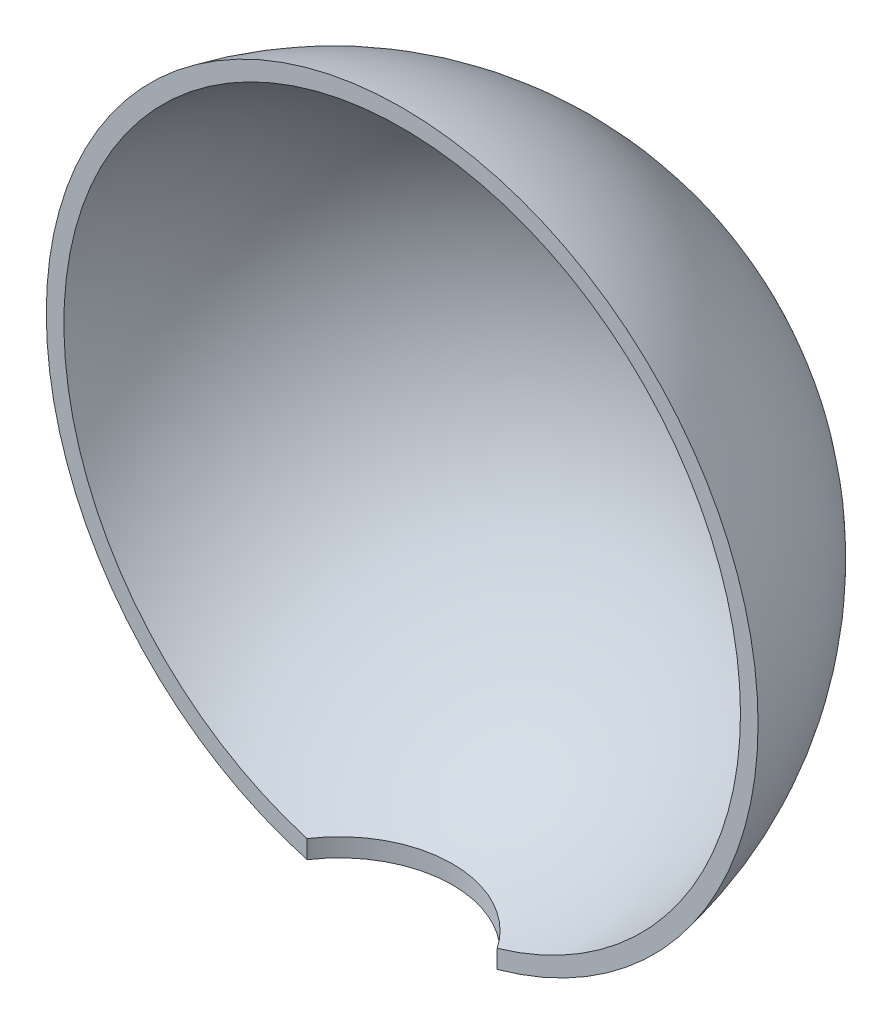
SolidWorks part; units mm, degrees
ref_plane "Front Plane" through (0, 0, 0) normal (0, 0, 1) x (1, 0, 0)
ref_plane "Top Plane" through (0, 0, 0) normal (0, 1, 0) x (1, 0, 0)
ref_plane "Right Plane" through (0, 0, 0) normal (1, 0, 0) x (0, 0, -1)
sketch "Sketch2" plane through (0, 0, 0) normal (0, 1, 0) x (1, 0, 0)
  line L0 (0, 29.6358) -> (0, 5.6358)
  line L1 (0, 5.6358) -> (29.3939, 5.6358)
  arc A0 (0, 29.6358) -> (29.3939, 5.6358) centre (0, -0.3642) cw
  dimension "D1" = 30
  dimension "D2" = 24
revolve "Revolve1" add sketch "Sketch2" angle 360 about L0
shell "Shell1" thickness 1.5
sketch "Sketch3" plane through (0, 0, 0) normal (0, 1, 0) x (1, 0, 0)
  circle A0 centre (0, 0) radius 10
  dimension "D1" = 20
extrude "Cut-Extrude1" cut sketch "Sketch3" against normal up to next
